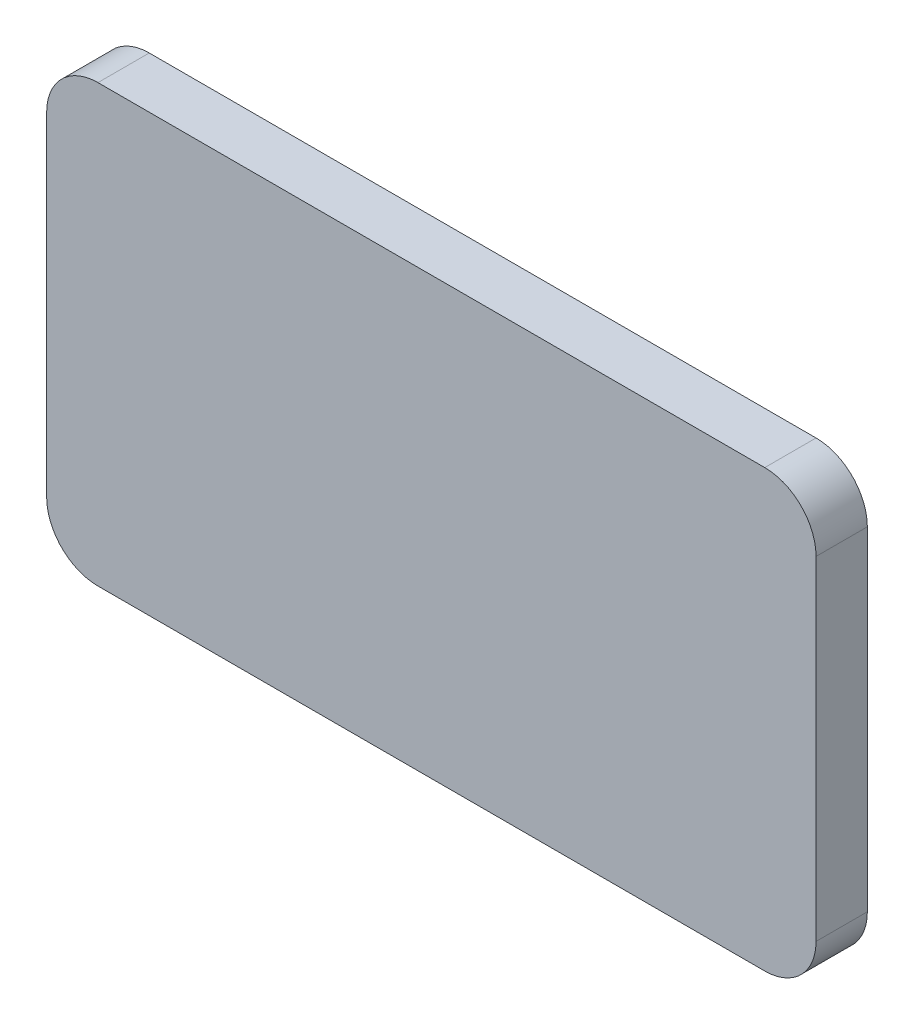
SolidWorks part; units mm, degrees
ref_plane "정면" through (0, 0, 0) normal (0, 0, 1) x (1, 0, 0)
ref_plane "윗면" through (0, 0, 0) normal (0, 1, 0) x (1, 0, 0)
ref_plane "우측면" through (0, 0, 0) normal (1, 0, 0) x (0, 0, -1)
sketch "스케치1" plane through (0, 0, 0) normal (0, 0, 1) x (1, 0, 0)
  line L0 (240.5972, 388.1466) -> (1204.5972, 388.1466) construction
  line L1 (0, 0) -> (30, 0)
  line L2 (0, 0) -> (0, -17)
  line L3 (0, -17) -> (30, -17)
  line L4 (30, 0) -> (30, -17)
extrude "보스-돌출1" add sketch "스케치1" along normal blind 2
fillet "필렛1" radius 2 4 edges at (0, 0, 1) (0, -17, 1) (30, -17, 1) (30, 0, 1)
